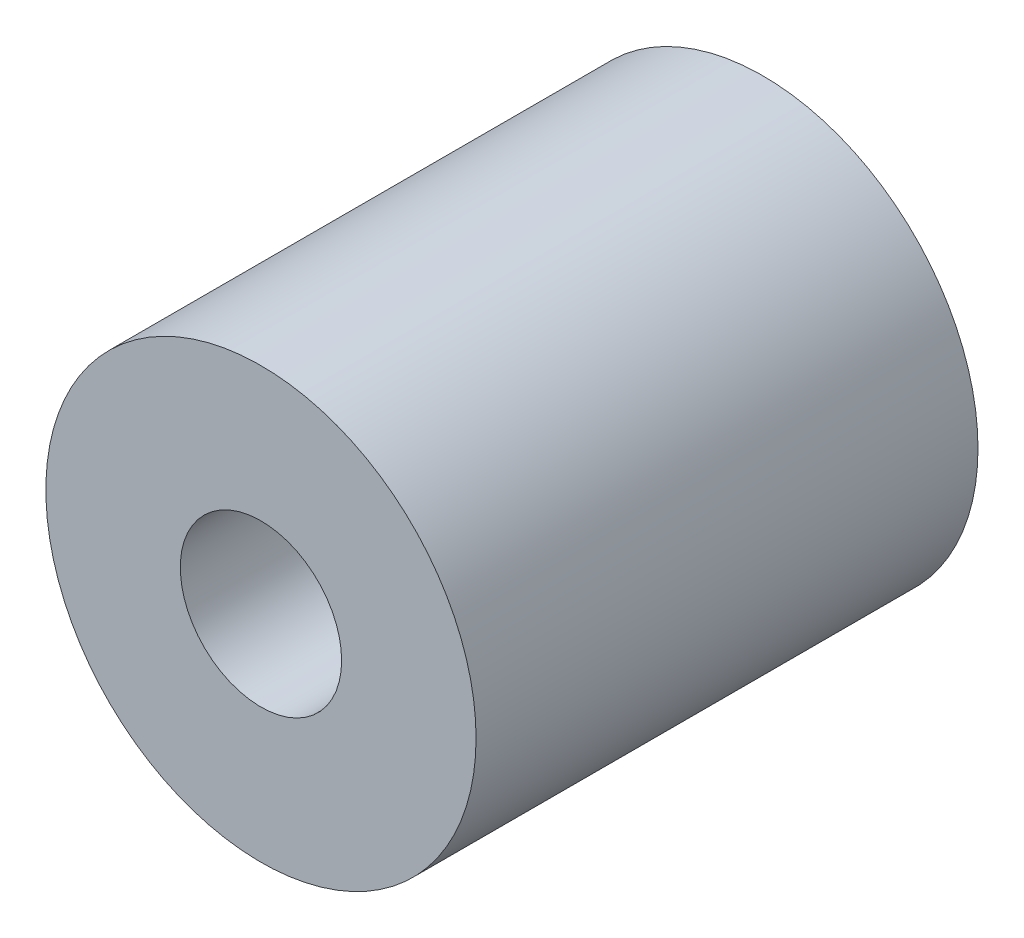
SolidWorks part; units mm, degrees
material "SS 304 (Default)"
ref_plane "Front Plane" through (0, 0, 0) normal (0, 0, 1) x (1, 0, 0)
ref_plane "Top Plane" through (0, 0, 0) normal (0, 1, 0) x (1, 0, 0)
ref_plane "Right Plane" through (0, 0, 0) normal (1, 0, 0) x (0, 0, -1)
sketch "Sketch1" plane through (0, 0, 0) normal (0, 0, 1) x (1, 0, 0)
  circle A0 centre (0, 0) radius 9.525
  circle A1 centre (0, 0) radius 3.5719
  dimension "D1" = 7.1437
  dimension "Diameter" = 19.05
extrude "Extrude1" add sketch "Sketch1" along normal mid plane 22.225
